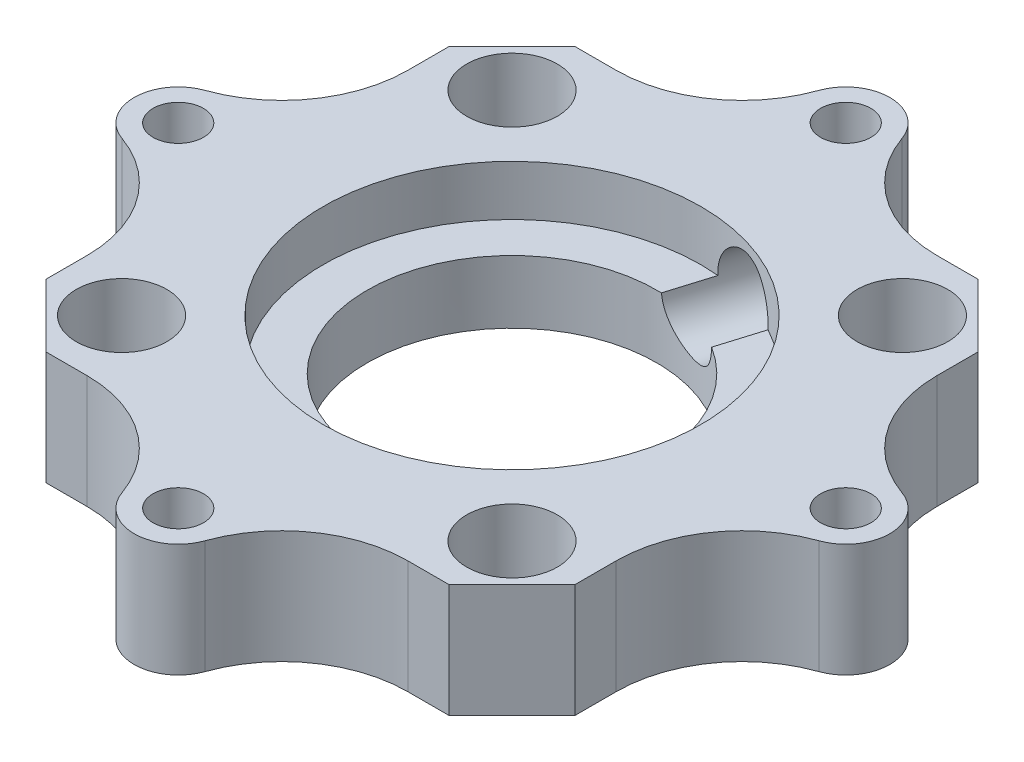
SolidWorks part; units mm, degrees
ref_plane "Front Plane" through (0, 0, 0) normal (0, 0, 1) x (1, 0, 0)
ref_plane "Top Plane" through (0, 0, 0) normal (0, 1, 0) x (1, 0, 0)
ref_plane "Right Plane" through (0, 0, 0) normal (1, 0, 0) x (0, 0, -1)
sketch "Sketch1" plane through (0, 0, 0) normal (0, 1, 0) x (1, 0, 0)
  line L1 (-30, -30) -> (30, -30)
  line L2 (-30, -30) -> (-30, 30)
  line L3 (-30, 30) -> (30, 30)
  line L4 (30, -30) -> (30, 30)
  line L5 (-30, -30) -> (30, 30) construction
  line L6 (-30, 30) -> (30, -30) construction
  circle A0 centre (0, 0) radius 11.5
  point P0 (0, 0)
  dimension "D2" = 23
  dimension "D1" = 60
extrude "Boss-Extrude1" add sketch "Sketch1" along normal blind 5
sketch "Sketch2" plane through (0, 5, 0) normal (0, 1, 0) x (1, 0, 0)
  line L1 (30, -30) -> (-30, -30)
  line L2 (30, -30) -> (30, 30)
  line L3 (30, 30) -> (-30, 30)
  line L4 (-30, -30) -> (-30, 30)
  line L5 (30, -30) -> (-30, 30) construction
  line L6 (30, 30) -> (-30, -30) construction
  circle A0 centre (0, 0) radius 30
  line M1 (30, -30) -> (30, 30)
  line M2 (30, 30) -> (-30, 30)
  line M3 (-30, 30) -> (-30, -30)
  line M4 (-30, -30) -> (30, -30)
extrude "Cut-Extrude1" cut sketch "Sketch2" against normal blind 10 contours A0 L3 M3 | A0 L2 M2 | A0 L1 M1 | A0 L4 M4
sketch "Sketch3" plane through (0, 5, 0) normal (0, 1, 0) x (1, 0, 0)
  line L0 (-12.9544, 12.9544) -> (0, 0) construction
  line L1 (-11.9, -15.5) -> (11.9, -15.5) construction
  line L2 (-15.5, -11.9) -> (-15.5, 11.9) construction
  line L3 (-11.9, 15.5) -> (11.9, 15.5) construction
  line L4 (15.5, -11.9) -> (15.5, 11.9) construction
  line L5 (-12.9544, -12.9544) -> (12.9544, 12.9544) construction
  line L6 (0, 0) -> (12.9544, -12.9544) construction
  line L7 (11.9, 15.5) -> (15.5, 15.5) construction
  line L8 (12.9544, 12.9544) -> (15.5, 15.5) construction
  line L9 (15.5, 11.9) -> (15.5, 15.5) construction
  line L10 (-15.5, 15.5) -> (-11.9, 15.5) construction
  line L11 (-15.5, 15.5) -> (-12.9544, 12.9544) construction
  line L12 (-15.5, 11.9) -> (-15.5, 15.5) construction
  line L13 (-15.5, -15.5) -> (-11.9, -15.5) construction
  line L14 (-15.5, -15.5) -> (-12.9544, -12.9544) construction
  line L15 (-15.5, -15.5) -> (-15.5, -11.9) construction
  line L16 (11.9, -15.5) -> (15.5, -15.5) construction
  line L17 (12.9544, -12.9544) -> (15.5, -15.5) construction
  line L18 (15.5, -15.5) -> (15.5, -11.9) construction
  circle A0 centre (-15.5, 15.5) radius 3.6
  circle A1 centre (15.5, 15.5) radius 3.6
  circle A2 centre (15.5, -15.5) radius 3.6
  circle A3 centre (-15.5, -15.5) radius 3.6
  arc A4 (-15.5, 15.5) -> (-17.828, 12.754) centre (0, 0) ccw construction
  arc A5 (12.754, 17.828) -> (-12.754, 17.828) centre (0, 0) ccw construction
  arc A6 (-17.828, 12.754) -> (-17.828, -12.754) centre (0, 0) ccw construction
  arc A7 (-17.828, -12.754) -> (-15.5, -15.5) centre (0, 0) ccw construction
  arc A8 (-12.754, -17.828) -> (12.754, -17.828) centre (0, 0) ccw construction
  arc A9 (15.5, -15.5) -> (17.828, -12.754) centre (0, 0) ccw construction
  arc A10 (17.828, -12.754) -> (17.828, 12.754) centre (0, 0) ccw construction
  arc A11 (17.828, 12.754) -> (15.5, 15.5) centre (0, 0) ccw construction
  arc A12 (15.5, 15.5) -> (12.754, 17.828) centre (0, 0) ccw construction
  arc A13 (-12.754, 17.828) -> (-15.5, 15.5) centre (0, 0) ccw construction
  arc A14 (-15.5, -15.5) -> (-12.754, -17.828) centre (0, 0) ccw construction
  arc A15 (12.754, -17.828) -> (15.5, -15.5) centre (0, 0) ccw construction
  point P0 (0, 0)
  point P17 (0, 0)
  dimension "D2" = 7.2
  dimension "D1" = 31
  dimension "D3" = 4
extrude "Cut-Extrude2" cut sketch "Sketch3" against normal blind 3
sketch "Sketch4" plane through (0, 2, 0) normal (0, 1, 0) x (1, 0, 0)
  circle A0 centre (-15.5, 15.5) radius 1.6
  circle A1 centre (15.5, 15.5) radius 1.6
  circle A2 centre (15.5, -15.5) radius 1.6
  circle A3 centre (-15.5, -15.5) radius 1.6
  point P12 (0, 0)
  dimension "D1" = 3.2
  dimension "D2" = 4
extrude "Cut-Extrude3" cut sketch "Sketch4" against normal blind 3
sketch "Sketch5" plane through (0, 5, 0) normal (0, 1, 0) x (1, 0, 0)
  line L0 (0, 30) -> (0, -30) construction
  line L1 (-23, 0) -> (23, 0) construction
  line L2 (-30, 0) -> (-23, 0) construction
  arc A0 (-30, 0) -> (-23, 0) centre (-26.5, 0) ccw construction
  arc A1 (-23, 0) -> (-30, 0) centre (-26.5, 0) ccw construction
  circle A2 centre (-26.5, 0) radius 2
  circle A3 centre (0, 26.5) radius 2
  circle A4 centre (26.5, 0) radius 2
  circle A5 centre (0, -26.5) radius 2
  point P5 (0, 0)
  point P6 (0, 0)
  point P19 (0, 0)
  dimension "D2" = 7
  dimension "D3" = 4
  dimension "D1" = 60
  dimension "D4" = 4
extrude "Cut-Extrude4" cut sketch "Sketch5" against normal through all
sketch "Sketch6" plane through (0, 5, 0) normal (0, 1, 0) x (1, 0, 0)
  line L0 (3.5, 21) -> (21, 21)
  line L1 (-26.5, 3.5) -> (-21, 3.5)
  line L2 (-26.5, -3.5) -> (-21, -3.5)
  line L3 (21, 3.5) -> (21, 21)
  line L4 (3.5, 26.5) -> (3.5, 21)
  line L5 (-3.5, 26.5) -> (-3.5, 21)
  line L6 (3.5, -21) -> (21, -21)
  line L7 (-21, -21) -> (-3.5, -21)
  line L8 (-21, -21) -> (-21, -3.5)
  line L9 (-21, 21) -> (-3.5, 21)
  line L10 (21, -21) -> (21, -3.5)
  line L11 (-21, 3.5) -> (-21, 21)
  line L15 (-3.5, -21) -> (-3.5, -26.5)
  line L17 (3.5, -21) -> (3.5, -26.5)
  line L18 (21, -3.5) -> (26.5, -3.5)
  line L20 (21, 3.5) -> (26.5, 3.5)
  arc A0 (-26.5, 3.5) -> (-26.5, -3.5) centre (-26.5, 0) ccw
  arc A1 (26.5, -3.5) -> (26.5, 3.5) centre (26.5, 0) ccw
  arc A2 (3.5, 26.5) -> (-3.5, 26.5) centre (0, 26.5) ccw
  arc A3 (-3.5, -26.5) -> (3.5, -26.5) centre (0, -26.5) ccw
  circle A4 centre (0, 0) radius 30
  point P4 (0, 0)
  point P9 (0, 0)
  point P18 (0, 0)
  circle M23 centre (0, 0) radius 30
  dimension "D1" = 3.5
  dimension "D2" = 3.5
  dimension "D3" = 42
extrude "Cut-Extrude5" cut sketch "Sketch6" against normal through all contours A2 A0 L1 L11 L9 L5 M23 | A2 L4 L0 L3 L20 A1 M23 | A3 L15 L7 L8 L2 A0 M23 | A3 A1 L18 L10 L6 L17 M23
chamfer "Chamfer1" distance 5 angle 45 4 edges at (-21, 2.5, -21) (-21, 2.5, 21) (21, 2.5, 21) (21, 2.5, -21)
fillet "Fillet1" radius 10 8 edges at (3.5, 2.5, -21) (-3.5, 2.5, -21) (-21, 2.5, -3.5) (-21, 2.5, 3.5) (-3.5, 2.5, 21) (3.5, 2.5, 21) (21, 2.5, 3.5) (21, 2.5, -3.5)
sketch "Sketch7" plane through (0, 5, 0) normal (0, 1, 0) x (1, 0, 0)
  line L12 (-21, -12.7279) -> (-21, -16)
  line L13 (-21, -16) -> (-16, -21)
  line L14 (-16, -21) -> (-12.7279, -21)
  line L15 (12.7279, -21) -> (16, -21)
  line L16 (16, -21) -> (21, -16)
  line L17 (21, -16) -> (21, -12.7279)
  line L18 (21, 12.7279) -> (21, 16)
  line L19 (21, 16) -> (16, 21)
  line L20 (16, 21) -> (12.7279, 21)
  line L21 (-12.7279, 21) -> (-16, 21)
  line L22 (-16, 21) -> (-21, 16)
  line L23 (-21, 16) -> (-21, 12.7279)
  line L24 (-21, -12.7279) -> (-21, -16)
  line L25 (-21, -16) -> (-16, -21)
  line L26 (-16, -21) -> (-12.7279, -21)
  line L27 (12.7279, -21) -> (16, -21)
  line L28 (16, -21) -> (21, -16)
  line L29 (21, -16) -> (21, -12.7279)
  line L30 (21, 12.7279) -> (21, 16)
  line L31 (21, 16) -> (16, 21)
  line L32 (16, 21) -> (12.7279, 21)
  line L33 (-12.7279, 21) -> (-16, 21)
  line L34 (-16, 21) -> (-21, 16)
  line L35 (-21, 16) -> (-21, 12.7279)
  circle A0 centre (-26.5, 0) radius 2
  circle A1 centre (0, 26.5) radius 2
  circle A2 centre (26.5, 0) radius 2
  circle A3 centre (0, -26.5) radius 2
  circle A4 centre (-15.5, 15.5) radius 3.6
  circle A5 centre (15.5, 15.5) radius 3.6
  circle A6 centre (15.5, -15.5) radius 3.6
  circle A7 centre (-15.5, -15.5) radius 3.6
  circle A8 centre (0, 0) radius 11.5
  arc A12 (-3.2998, -27.6667) -> (-12.7279, -21) centre (-12.7279, -31) ccw
  arc A13 (-3.2998, -27.6667) -> (3.2998, -27.6667) centre (0, -26.5) ccw
  arc A14 (12.7279, -21) -> (3.2998, -27.6667) centre (12.7279, -31) ccw
  arc A15 (27.6667, -3.2998) -> (21, -12.7279) centre (31, -12.7279) ccw
  arc A16 (27.6667, -3.2998) -> (27.6667, 3.2998) centre (26.5, 0) ccw
  arc A17 (21, 12.7279) -> (27.6667, 3.2998) centre (31, 12.7279) ccw
  arc A18 (3.2998, 27.6667) -> (12.7279, 21) centre (12.7279, 31) ccw
  arc A19 (3.2998, 27.6667) -> (-3.2998, 27.6667) centre (0, 26.5) ccw
  arc A20 (-12.7279, 21) -> (-3.2998, 27.6667) centre (-12.7279, 31) ccw
  arc A21 (-27.6667, 3.2998) -> (-21, 12.7279) centre (-31, 12.7279) ccw
  arc A22 (-27.6667, 3.2998) -> (-27.6667, -3.2998) centre (-26.5, 0) ccw
  arc A23 (-21, -12.7279) -> (-27.6667, -3.2998) centre (-31, -12.7279) ccw
  arc A24 (-3.2998, -27.6667) -> (-12.7279, -21) centre (-12.7279, -31) ccw
  arc A25 (-3.2998, -27.6667) -> (3.2998, -27.6667) centre (0, -26.5) ccw
  arc A26 (12.7279, -21) -> (3.2998, -27.6667) centre (12.7279, -31) ccw
  arc A27 (27.6667, -3.2998) -> (21, -12.7279) centre (31, -12.7279) ccw
  arc A28 (27.6667, -3.2998) -> (27.6667, 3.2998) centre (26.5, 0) ccw
  arc A29 (21, 12.7279) -> (27.6667, 3.2998) centre (31, 12.7279) ccw
  arc A30 (3.2998, 27.6667) -> (12.7279, 21) centre (12.7279, 31) ccw
  arc A31 (3.2998, 27.6667) -> (-3.2998, 27.6667) centre (0, 26.5) ccw
  arc A32 (-12.7279, 21) -> (-3.2998, 27.6667) centre (-12.7279, 31) ccw
  arc A33 (-27.6667, 3.2998) -> (-21, 12.7279) centre (-31, 12.7279) ccw
  arc A34 (-27.6667, 3.2998) -> (-27.6667, -3.2998) centre (-26.5, 0) ccw
  arc A35 (-21, -12.7279) -> (-27.6667, -3.2998) centre (-31, -12.7279) ccw
  point P39 (0, 0)
  point P54 (0, 0)
  dimension "D1" = 0
  dimension "D2" = 4
  dimension "D3" = 4
extrude "Boss-Extrude2" add sketch "Sketch7" along normal blind 4
sketch "Sketch8" plane through (0, 9, 0) normal (0, 1, 0) x (1, 0, 0)
  circle A0 centre (0, 0) radius 15
  dimension "D1" = 30
extrude "Cut-Extrude6" cut sketch "Sketch8" against normal blind 4
sketch "Sketch9" plane through (0, 9, 0) normal (0, 1, 0) x (1, 0, 0)
  line L0 (0, 0) -> (30, 0) construction
  line L1 (0, 0) -> (0, 30) construction
  line L2 (0, 30) -> (6.9544, 22.835) construction
  line L3 (6.9544, 22.835) -> (0, 0) construction
  arc A0 (27.6667, -3.2998) -> (27.6667, 3.2998) centre (26.5, 0) ccw construction
  arc A1 (3.2998, 27.6667) -> (-3.2998, 27.6667) centre (0, 26.5) ccw construction
  arc A2 (3.2998, 27.6667) -> (12.7279, 21) centre (12.7279, 31) ccw construction
ref_plane "Plane1" through (6.8067, 0, -22.3499) normal (0.2913, 0, -0.9566) x (-0.9566, 0, -0.2913)
sketch "Sketch10" plane through (6.8067, 0, -22.3499) normal (0.2913, 0, -0.9566) x (-0.9566, 0, -0.2913)
  line L0 (0, 8.9079) -> (0, 0) construction
  circle A0 centre (0, 5.2353) radius 3
  dimension "D1" = 6
extrude "Cut-Extrude7" cut sketch "Sketch10" against normal blind 16 and the other way blind 10
sketch "Sketch11" plane through (0, 0, 0) normal (0, -1, 0) x (1, 0, 0)
  point P0 (0, 0)
